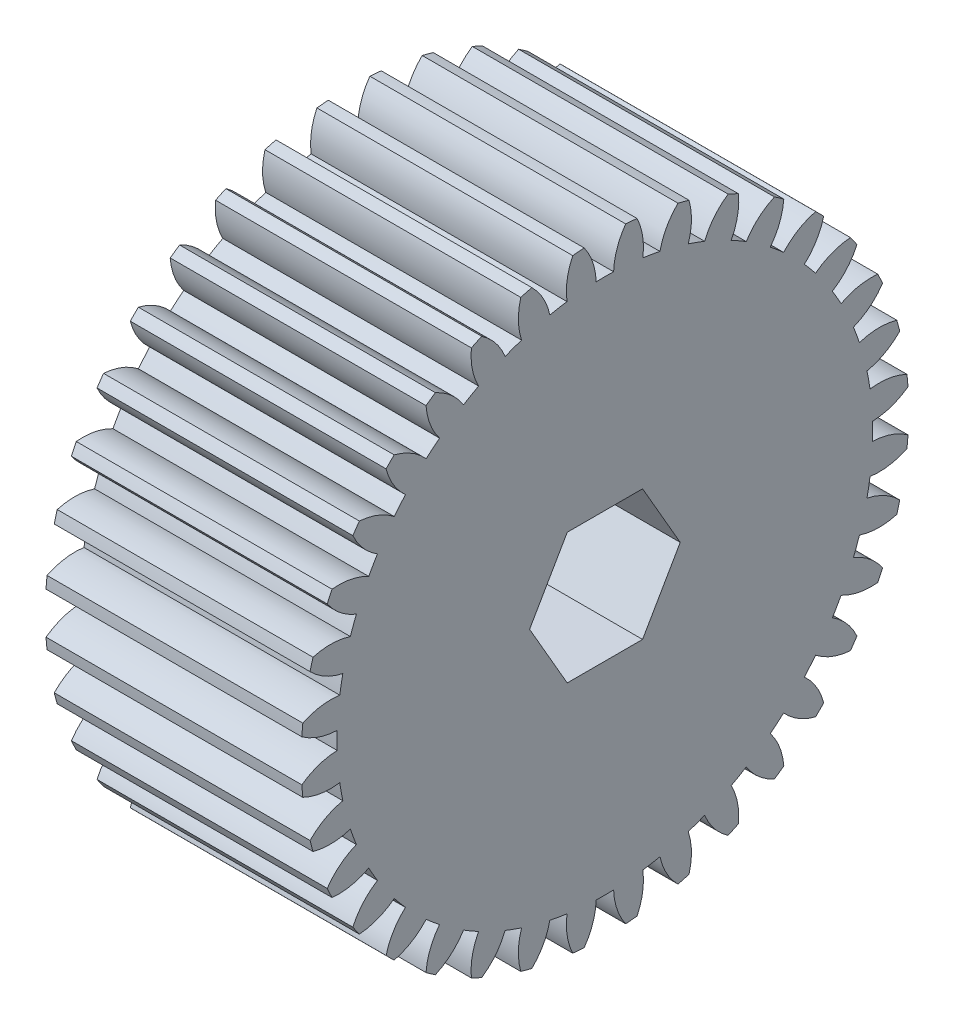
SolidWorks part; units mm, degrees
material "ABS"
ref_plane "Front Plane" through (0, 0, 0) normal (0, 0, 1) x (1, 0, 0)
ref_plane "Top Plane" through (0, 0, 0) normal (0, 1, 0) x (1, 0, 0)
ref_plane "Right Plane" through (0, 0, 0) normal (1, 0, 0) x (0, 0, -1)
sketch "Sketch1" plane through (0, 0, 0) normal (1, 0, 0) x (0, 0, -1)
  circle A0 centre (0, 0) radius 28.575
  circle A1 centre (0, 0) radius 30.1625
  circle A2 centre (0, 0) radius 26.5906
  dimension "D1" = 57.15
  dimension "D2" = 1.5875
  dimension "D3" = 3.5719
extrude "Boss-Extrude1" add sketch "Sketch1" along normal blind 25.4 contours A2 | A0 A2 | A1 A0
sketch "Sketch2" plane through (25.4, 0, 0) normal (1, 0, 0) x (0, 0, -1)
  line L0 (0, 0) -> (0, 30.1625) construction
  line L1 (0, 25.1233) -> (-1.2464, 28.5478) construction
  line L2 (-1.2464, 28.5478) -> (1.2464, 28.5478) construction
  line L3 (1.2464, 28.5478) -> (3.7298, 28.3305) construction
  line L4 (2.4881, 28.4392) -> (0, 0) construction
  line L5 (-0.8656, 26.5765) -> (0, 0) construction
  circle A0 centre (0, 0) radius 30.1625 construction
  arc A1 (-0.8656, 26.5765) -> (-2.6937, 30.8388) centre (-7.2322, 26.3692) ccw
  circle A2 centre (0, 0) radius 26.5906
  arc A3 (0.8656, 26.5765) -> (-0.8656, 26.5765) centre (0, 0) ccw
  circle A4 centre (0, 0) radius 30.1625
  circle A5 centre (0, 0) radius 30.1625 construction
  circle A6 centre (0, 0) radius 28.575
  circle A7 centre (0, 0) radius 28.575 construction
  arc A8 (2.6937, 30.8388) -> (-2.6937, 30.8388) centre (0, 0) ccw
  arc A9 (0.8656, 26.5765) -> (2.6937, 30.8388) centre (7.2322, 26.3692) cw
  dimension "D4" = 0.7937
  dimension "D5" = 5
  dimension "D6" = 20
  dimension "D1" = 0
extrude "Cut-Extrude1" cut sketch "Sketch2" against normal through all
pattern_circular "CirPattern1" count 36 over 360 about axis through (0, 0, 0) along (1, 0, 0) of "Cut-Extrude1"
sketch "Sketch3" plane through (25.4, 0, 0) normal (1, 0, 0) x (0, 0, -1)
  line L1 (3.7395, 6.477) -> (-3.7395, 6.477)
  line L2 (-3.7395, 6.477) -> (-7.479, 0)
  line L3 (-7.479, 0) -> (-3.7395, -6.477)
  line L4 (-3.7395, -6.477) -> (3.7395, -6.477)
  line L5 (3.7395, -6.477) -> (7.479, 0)
  line L6 (7.479, 0) -> (3.7395, 6.477)
  circle A0 centre (0, 0) radius 6.477 construction
  dimension "D1" = 12.954
extrude "Cut-Extrude2" cut sketch "Sketch3" against normal through all
sketch "Sketch4" plane through (25.4, 0, 0) normal (1, 0, 0) x (0, 0, -1)
  circle A0 centre (0, 0) radius 28.575
  dimension "D1" = 57.15
equation "\"Module\"= 1 / 16in"
equation "\"Number of Teeth\"= 36"
equation "\"D1@Sketch1\"=\"Module\" * \"Number of Teeth\""
equation "\"D2@Sketch1\"=\"Module\""
equation "\"D3@Sketch1\"=2.25 * \"Module\""
equation "\"D5@Sketch2\"=180 / \"Number of Teeth\""
equation "\"D1@CirPattern1\"=\"Number of Teeth\""
equation "\"D1@Sketch4\"=\"Module\" * \"Number of Teeth\""
